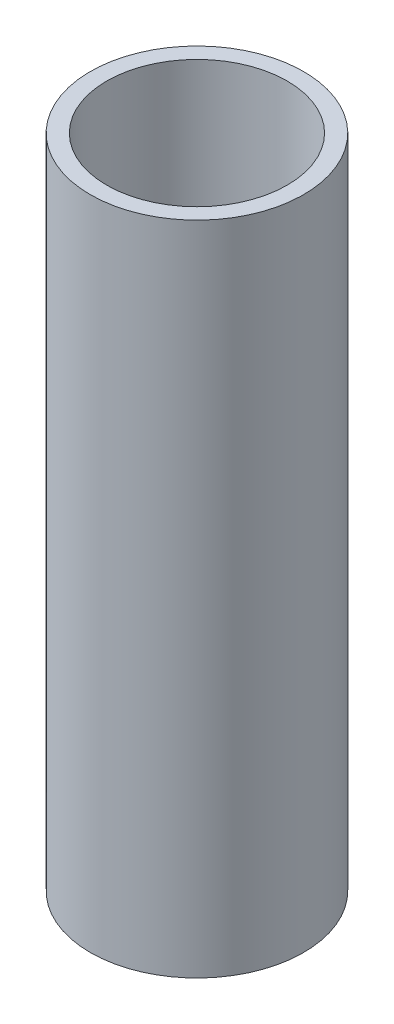
SolidWorks part; units mm, degrees
ref_plane "Plan de face" through (0, 0, 0) normal (0, 0, 1) x (1, 0, 0)
ref_plane "Plan de dessus" through (0, 0, 0) normal (0, 1, 0) x (1, 0, 0)
ref_plane "Plan de droite" through (0, 0, 0) normal (1, 0, 0) x (0, 0, -1)
sketch "Esquisse1" plane through (0, 0, 0) normal (0, 1, 0) x (1, 0, 0)
  circle A0 centre (0, 0) radius 11
  circle A1 centre (0, 0) radius 13
  dimension "D1" = 22
  dimension "D2" = 26
extrude "Boss.-Extru.1" add sketch "Esquisse1" along normal blind 80
